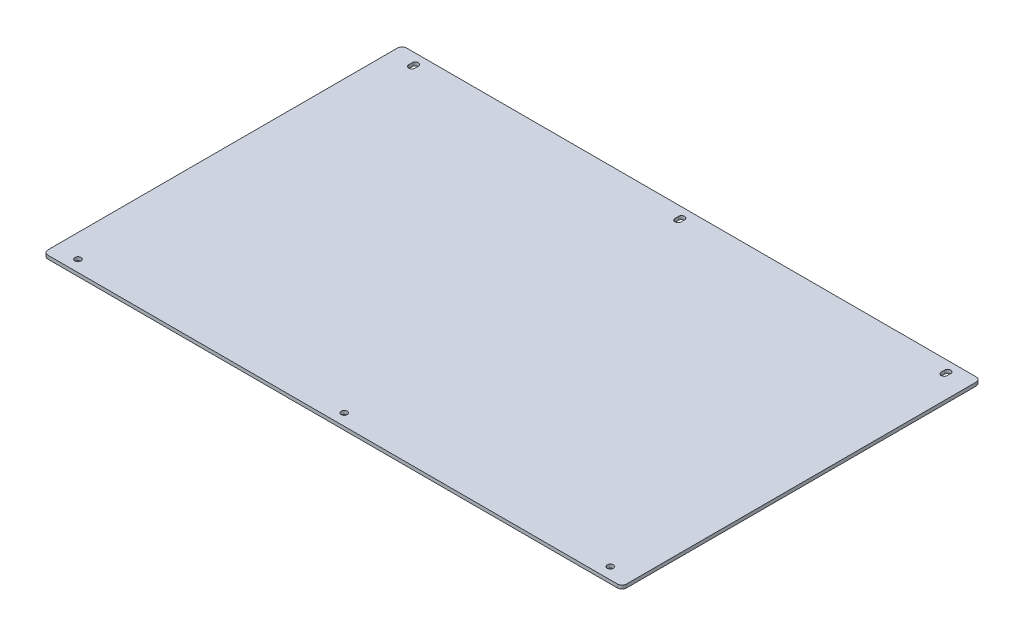
SolidWorks part; units mm, degrees
ref_plane "Front Plane" through (0, 0, 0) normal (0, 0, 1) x (1, 0, 0)
ref_plane "Top Plane" through (0, 0, 0) normal (0, 1, 0) x (1, 0, 0)
ref_plane "Right Plane" through (0, 0, 0) normal (1, 0, 0) x (0, 0, -1)
sketch "Sketch1" plane through (0, 0, 0) normal (0, 1, 0) x (1, 0, 0)
  line L1 (-250, -155) -> (250, -155)
  line L2 (-250, -155) -> (-250, 155)
  line L3 (-250, 155) -> (250, 155)
  line L4 (250, -155) -> (250, 155)
  line L5 (-250, -155) -> (250, 155) construction
  line L6 (-250, 155) -> (250, -155) construction
  point P0 (0, 0)
  dimension "D1" = 500
  dimension "D2" = 310
extrude "Boss-Extrude1" add sketch "Sketch1" along normal blind 3
fillet "Fillet1" radius 4 4 edges at (-250, 1.5, 155) (-250, 1.5, -155) (250, 1.5, -155) (250, 1.5, 155)
hole_wizard "Ø5.3 (5.3) Diameter Hole1" positions "Sketch4" profile "Sketch5" hole size "Ø5.3" standard "ANSI Metric" end condition through all
sketch "Sketch4" plane through (0, 3, 0) normal (0, 1, 0) x (1, 0, 0)
  line L1 (-230, -145) -> (230, -145)
  line L2 (-230, -145) -> (-230, 145)
  line L3 (-230, 145) -> (230, 145)
  line L4 (230, -145) -> (230, 145)
  line L5 (-230, -145) -> (230, 145) construction
  line L6 (-230, 145) -> (230, -145) construction
  line L7 (246, 155) -> (-246, 155) construction
  line L8 (250, -151) -> (250, 151) construction
  point P2 (230, 145)
  point P59 (-230, -145)
  point P60 (-230, 145)
  point P61 (230, -145)
  point P68 (0, 145)
  point P70 (0, -145)
  dimension "D1" = 10
  dimension "D2" = 20
sketch "Sketch5" plane through (230, 3, -145) normal (1, 0, 0) x (0, 0, 1)
  line L0 (0, 0) -> (0, 3)
  line L1 (0, 3) -> (2.65, 3)
  line L2 (2.65, 3) -> (2.65, 0)
  line L5 (2.65, 0) -> (0, 0)
  line L11 (0, -6.35) -> (0, 107.95) construction
  dimension "Thru Hole Dia." = 5.3
  dimension "Thru Hole Depth" = 3
sketch "Sketch6" plane through (0, 3, 0) normal (0, 1, 0) x (1, 0, 0)
  line L0 (-230, 143.5) -> (-230, 146.5) construction
  line L1 (-232.65, 143.5) -> (-232.65, 146.5)
  line L2 (-227.35, 143.5) -> (-227.35, 146.5)
  line L3 (0, 143.5) -> (0, 146.5) construction
  line L4 (-2.65, 143.5) -> (-2.65, 146.5)
  line L5 (2.65, 143.5) -> (2.65, 146.5)
  line L6 (230, 143.5) -> (230, 146.5) construction
  line L7 (227.35, 143.5) -> (227.35, 146.5)
  line L8 (232.65, 143.5) -> (232.65, 146.5)
  arc A0 (-232.65, 143.5) -> (-227.35, 143.5) centre (-230, 143.5) ccw
  arc A1 (-227.35, 146.5) -> (-232.65, 146.5) centre (-230, 146.5) ccw
  circle A2 centre (-230, 145) radius 2.65 construction
  arc A3 (-2.65, 143.5) -> (2.65, 143.5) centre (0, 143.5) ccw
  arc A4 (2.65, 146.5) -> (-2.65, 146.5) centre (0, 146.5) ccw
  arc A5 (227.35, 143.5) -> (232.65, 143.5) centre (230, 143.5) ccw
  arc A6 (232.65, 146.5) -> (227.35, 146.5) centre (230, 146.5) ccw
  point P2 (-230, 145)
  point P10 (0, 145)
  point P14 (0, 145)
  point P21 (230, 145)
  dimension "D1" = 3
  dimension "D2" = 3
extrude "Cut-Extrude1" cut sketch "Sketch6" against normal through all
